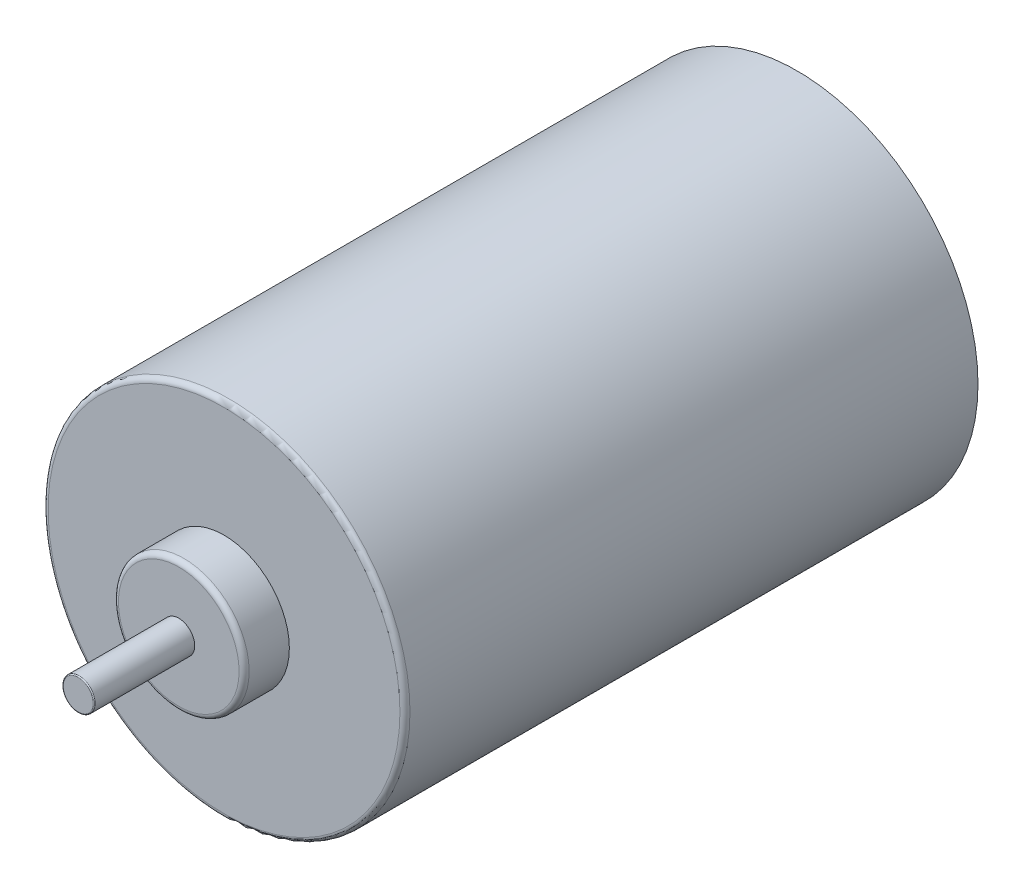
SolidWorks part; units mm, degrees
ref_plane "Front Plane" through (0, 0, 0) normal (0, 0, 1) x (1, 0, 0)
ref_plane "Top Plane" through (0, 0, 0) normal (0, 1, 0) x (1, 0, 0)
ref_plane "Right Plane" through (0, 0, 0) normal (1, 0, 0) x (0, 0, -1)
sketch "Sketch1" plane through (0, 0, 0) normal (0, 0, 1) x (1, 0, 0)
  circle A0 centre (0, 0) radius 18
  circle A1 centre (0, 0) radius 17
  dimension "D1" = 36
  dimension "D2" = 1
extrude "Boss-Extrude1" add sketch "Sketch1" along normal blind 57
sketch "Sketch4" plane through (0, 0, 0) normal (0, 0, -1) x (-1, 0, 0)
  circle A0 centre (0, 0) radius 18
  circle A2 centre (0, 0) radius 18 construction
extrude "Boss-Extrude4" add sketch "Sketch4" against normal blind 2
sketch "Sketch5" plane through (0, 0, 0) normal (0, 0, -1) x (-1, 0, 0)
  circle A0 centre (0, 0) radius 13
  dimension "D1" = 26
extrude "Boss-Extrude5" add sketch "Sketch5" along normal blind 2
sketch "Sketch6" plane through (0, 0, -2) normal (0, 0, -1) x (-1, 0, 0)
  circle A0 centre (0, 0) radius 1.5875
  dimension "D1" = 3.175
extrude "Cut-Extrude1" cut sketch "Sketch6" against normal up to surface (4 mm away) up to face at (-17, 0, 2)
sketch "Sketch7" plane through (0, 0, 57) normal (0, 0, 1) x (1, 0, 0)
  circle A0 centre (0, 0) radius 18
extrude "Boss-Extrude6" add sketch "Sketch7" against normal blind 1
sketch "Sketch8" plane through (0, 0, 57) normal (0, 0, 1) x (1, 0, 0)
  circle A0 centre (0, 0) radius 6.5
  dimension "D1" = 13
extrude "Boss-Extrude7" add sketch "Sketch8" along normal blind 4.5
sketch "Sketch9" plane through (0, 0, 61.5) normal (0, 0, 1) x (1, 0, 0)
  circle A0 centre (0, 0) radius 1.5875
  dimension "D1" = 3.175
extrude "Cut-Extrude4" cut sketch "Sketch9" against normal through all
sketch "Sketch10" plane through (0, 0, 61.5) normal (0, 0, 1) x (1, 0, 0)
  circle A0 centre (0, 0) radius 1.5875
extrude "Boss-Extrude8" add sketch "Sketch10" along normal blind 10 and the other way blind 65 separate body
fillet "Fillet1" radius 0.5 2 edges at (6.5, 0, 61.5) (18, 0, 57)
fillet "Fillet2" radius 0.1 1 edges at (1.5875, 0, 71.5)
chamfer "Chamfer1" distance 1 angle 45 1 edges at (-13, 0, -2)
fillet "Fillet3" radius 0.1 1 edges at (1.5875, 0, -3.5)
